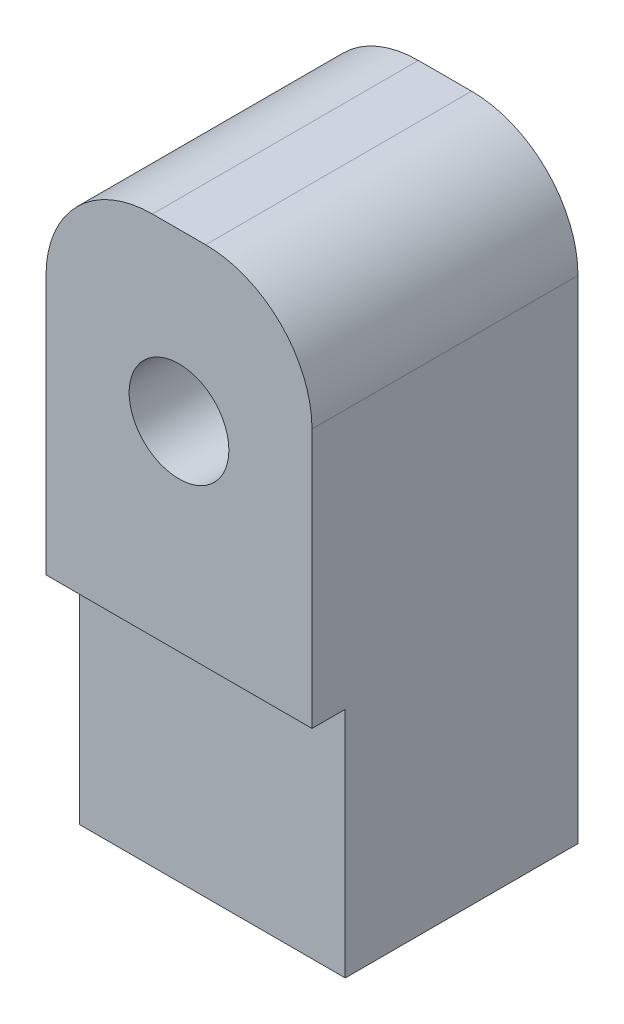
SolidWorks part; units mm, degrees
ref_plane "Front Plane" through (0, 0, 0) normal (0, 0, 1) x (1, 0, 0)
ref_plane "Top Plane" through (0, 0, 0) normal (0, 1, 0) x (1, 0, 0)
ref_plane "Right Plane" through (0, 0, 0) normal (1, 0, 0) x (0, 0, -1)
sketch "Sketch2" plane through (0, 0, 0) normal (0, 0, 1) x (1, 0, 0)
  line L0 (0, -11.25) -> (0, -2.5) construction
  line L1 (-5, 11.25) -> (5, 11.25)
  line L2 (-5, 11.25) -> (-5, -11.25)
  line L3 (-5, -11.25) -> (5, -11.25)
  line L4 (5, 11.25) -> (5, -11.25)
  line L5 (-5, -2.5) -> (5, -2.5)
  point P0 (0, 0)
  point P12 (0, -2.5)
  dimension "D1" = 22.5
  dimension "D2" = 8.75
extrude "Boss-Extrude1" add sketch "Sketch2" along normal blind 8.75 contours L0 L3 L4 L5 | L3 L0 L5 L2
sketch "Sketch3" plane through (0, -2.5, 0) normal (0, 1, 0) x (1, 0, 0)
  line L1 (-5, -10) -> (5, -10)
  line L2 (-5, -10) -> (-5, 0)
  line L3 (-5, 0) -> (5, 0)
  line L4 (5, -10) -> (5, 0)
  line L5 (-5, -10) -> (5, 0) construction
  line L6 (-5, 0) -> (5, -10) construction
  point P0 (0, -5)
  dimension "D1" = 10
  dimension "D2" = 10
extrude "Boss-Extrude2" add sketch "Sketch3" along normal blind 13.75
fillet "Fillet1" radius 4 2 edges at (-5, 11.25, 5) (5, 11.25, 5)
sketch "Sketch4" plane through (0, -11.25, 0) normal (0, -1, 0) x (1, 0, 0)
  line L0 (0, 0) -> (0, 5) construction
  circle A0 centre (0, 5) radius 2.5
  dimension "D1" = 5
extrude "Cut-Extrude1" cut sketch "Sketch4" against normal blind 11.88
sketch "Sketch5" plane through (0, 0, 10) normal (0, 0, 1) x (1, 0, 0)
  line L0 (0, 11.25) -> (0, 5) construction
  line L1 (-1, 11.25) -> (1, 11.25) construction
  circle A0 centre (0, 5) radius 1.875
  dimension "D2" = 3.75
  dimension "D1" = 6.25
extrude "Cut-Extrude2" cut sketch "Sketch5" against normal blind 8.75
sketch "Sketch6" plane through (0, 0, 0) normal (0, 0, -1) x (-1, 0, 0)
  line L0 (0, 11.25) -> (0, 5) construction
  line L1 (-1, 11.25) -> (1, 11.25) construction
  circle A0 centre (0, 5) radius 2.375
  dimension "D2" = 4.75
  dimension "D1" = 6.25
extrude "Cut-Extrude3" cut sketch "Sketch6" against normal blind 1.25
